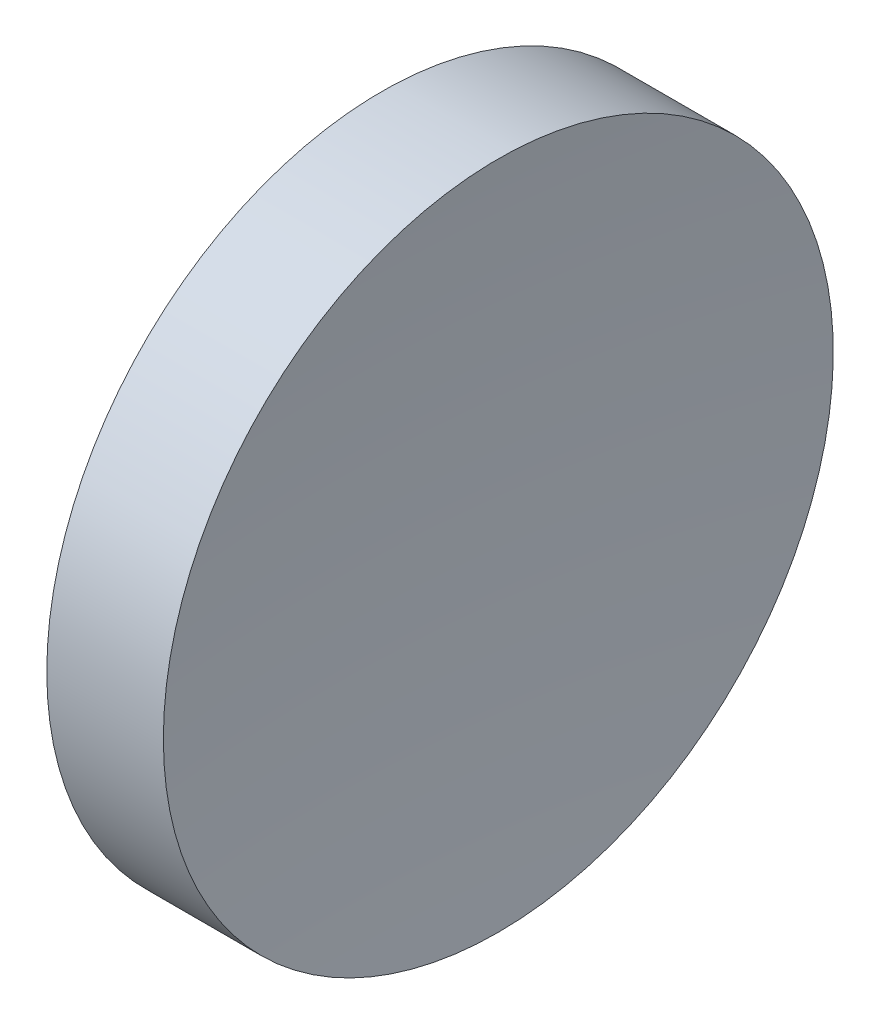
SolidWorks part; units mm, degrees
ref_plane "前视基准面" through (0, 0, 0) normal (0, 0, 1) x (1, 0, 0)
ref_plane "上视基准面" through (0, 0, 0) normal (0, 1, 0) x (1, 0, 0)
ref_plane "右视基准面" through (0, 0, 0) normal (1, 0, 0) x (0, 0, -1)
sketch "草图1" plane through (0, 0, 0) normal (0, 0, 1) x (1, 0, 0)
  line L0 (42.4499, 26.089) -> (50.324, 26.089) construction
  line L1 (44.3196, 26.089) -> (44.3196, 31.089)
  line L2 (45.8196, 26.089) -> (44.3196, 26.089)
  line L3 (44.3196, 31.089) -> (46.0596, 31.089)
  arc A0 (46.0596, 31.089) -> (45.8196, 26.089) centre (98.0229, 26.089) ccw
revolve "旋转1" add sketch "草图1" angle 360 about L0
